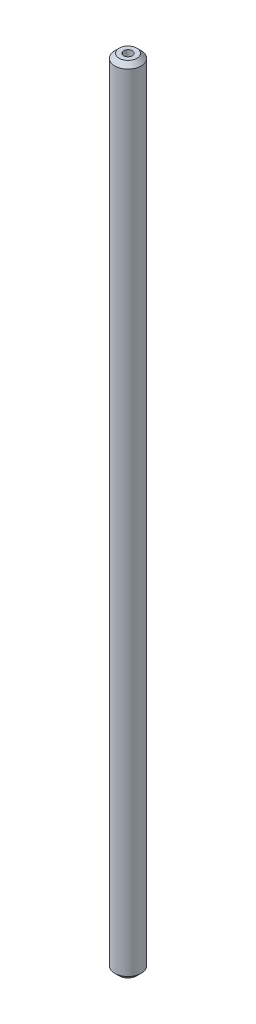
SolidWorks part; units mm, degrees
ref_plane "Front Plane" through (0, 0, 0) normal (0, 0, 1) x (1, 0, 0)
ref_plane "Top Plane" through (0, 0, 0) normal (0, 1, 0) x (1, 0, 0)
ref_plane "Right Plane" through (0, 0, 0) normal (1, 0, 0) x (0, 0, -1)
sketch "Sketch1" plane through (0, 0, 0) normal (0, 1, 0) x (1, 0, 0)
  circle A0 centre (0, 0) radius 0.5
  circle A1 centre (0, 0) radius 1.5
  dimension "D1" = 1
  dimension "D2" = 3
extrude "Boss-Extrude1" add sketch "Sketch1" along normal blind 90
chamfer "Chamfer1" distance 0.5 angle 45 2 edges at (0, 90, 1.5) (0, 0, 1.5)
